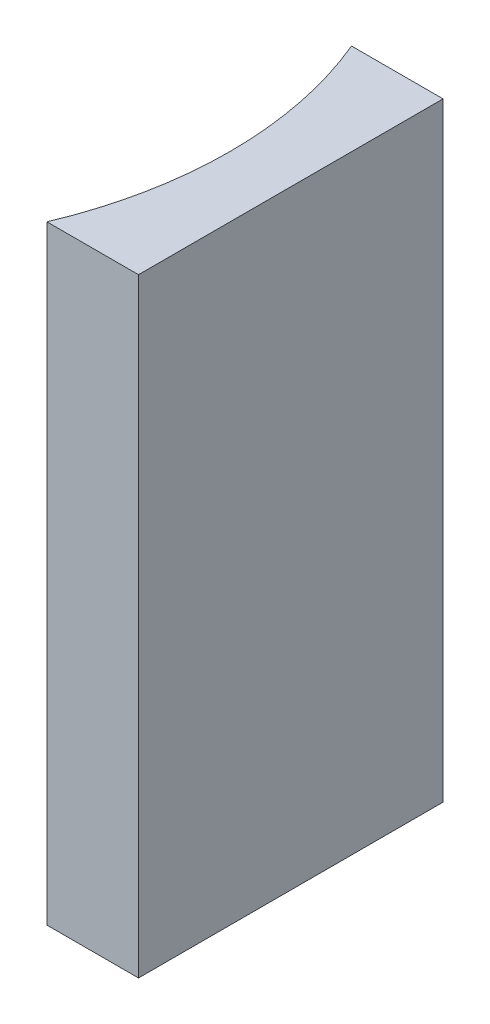
SolidWorks part; units mm, degrees
ref_plane "前视基准面" through (0, 0, 0) normal (0, 0, 1) x (1, 0, 0)
ref_plane "上视基准面" through (0, 0, 0) normal (0, 1, 0) x (1, 0, 0)
ref_plane "右视基准面" through (0, 0, 0) normal (1, 0, 0) x (0, 0, -1)
sketch "草图1" plane through (0, 0, 0) normal (0, 1, 0) x (1, 0, 0)
  line L0 (0, 0) -> (0, -10)
  line L1 (0, 0) -> (-3.0059, 0)
  line L2 (0, -10) -> (-3.0059, -10)
  line L3 (8.2336, -5) -> (-10.4405, -5) construction
  arc A0 (-3.0059, -10) -> (-3.0059, 0) centre (-14.93, -5) ccw
  point P7 (-2, -5)
  point P8 (0, -5)
  dimension "D2" = 12.93
  dimension "D3" = 2
  dimension "D1" = 10
extrude "凸台-拉伸1" add sketch "草图1" along normal blind 20
